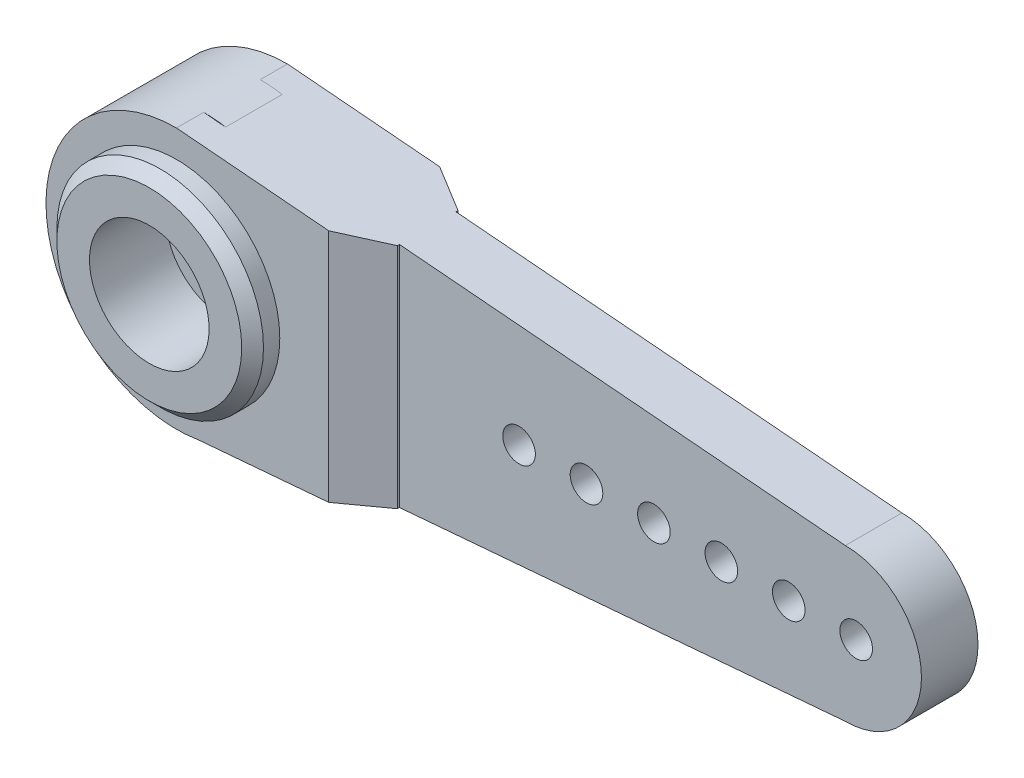
SolidWorks part; units mm, degrees
ref_plane "Front Plane" through (0, 0, 0) normal (0, 0, 1) x (1, 0, 0)
ref_plane "Top Plane" through (0, 0, 0) normal (0, 1, 0) x (1, 0, 0)
ref_plane "Right Plane" through (0, 0, 0) normal (1, 0, 0) x (0, 0, -1)
sketch "Sketch1" plane through (0, 0, 0) normal (0, 0, 1) x (1, 0, 0)
  line L0 (1.0097, 5.9144) -> (29.5, 3.5)
  line L1 (29.5, -3.5) -> (1.0097, -5.9144)
  arc A0 (1.0097, 5.9144) -> (1.0097, -5.9144) centre (0, 0) ccw
  arc A1 (29.5, -3.5) -> (29.5, 3.5) centre (29.5, 0) ccw
  point P5 (-6, 0)
  point P6 (33, 0)
  dimension "D3" = 39
extrude "Boss-Extrude1" add sketch "Sketch1" along normal blind 2.6
sketch "Sketch2" plane through (0, 0, 2.6) normal (0, 0, 1) x (1, 0, 0)
  circle A0 centre (0, 0) radius 4.75
  dimension "D1" = 9.5
extrude "Boss-Extrude2" add sketch "Sketch2" along normal blind 2.5
sketch "Sketch3" plane through (0, 0, 2.6) normal (0, 0, 1) x (1, 0, 0)
  circle A0 centre (0, 0) radius 2.5
  dimension "D1" = 5
extrude "Cut-Extrude1" cut sketch "Sketch3" along normal blind 4
sketch "Sketch4" plane through (0, 0, 2.6) normal (0, 0, 1) x (1, 0, 0)
  line L0 (33, 0) -> (0, 0) construction
  arc A0 (29.5, -3.5) -> (29.5, 3.5) centre (29.5, 0) ccw construction
  circle A1 centre (30, 0) radius 0.75
  circle A3 centre (26.9, 0) radius 0.75
  circle A4 centre (23.8, 0) radius 0.75
  circle A5 centre (20.7, 0) radius 0.75
  circle A6 centre (17.6, 0) radius 0.75
  circle A7 centre (14.5, 0) radius 0.75
  dimension "D1" = 1.5
  dimension "D2" = 3
  dimension "D4" = 3.1
  dimension "D3" = 6
extrude "Cut-Extrude2" cut sketch "Sketch4" against normal blind 4
sketch "Sketch5" plane through (0, 0, 2.6) normal (0, 0, 1) x (1, 0, 0)
  line L0 (0, 6) -> (9, 5.2373)
  line L1 (29.5, 3.5) -> (1.0097, 5.9144) construction
  line L2 (9, 5.2373) -> (9, -5.2373)
  line L3 (1.0097, -5.9144) -> (29.5, -3.5) construction
  line L4 (9, -5.2373) -> (1.0097, -5.9144)
  arc A0 (1.0097, 5.9144) -> (1.0097, -5.9144) centre (0, 0) ccw
  point P7 (8.7819, -5.2558)
  circle M7 centre (0, 0) radius 4.75
  arc M8 (1.0097, 5.9144) -> (1.0097, -5.9144) centre (0, 0) ccw
  line M9 (1.0097, -5.9144) -> (29.5, -3.5)
  line M11 (29.5, 3.5) -> (1.0097, 5.9144)
  dimension "D1" = 9
extrude "Boss-Extrude3" add sketch "Sketch5" along normal blind 1.25 contours L2 L0 M11 M8 M9 M7
chamfer "Chamfer1" distance 2 angle 30 1 edges at (9, 0, 3.85)
sketch "Sketch6" plane through (0, 0, 0) normal (0, 0, -1) x (-1, 0, 0)
  line L0 (0, -6) -> (-9, -5.2373)
  line L1 (-1.0097, -5.9144) -> (-29.5, -3.5) construction
  line L2 (-9, -5.2373) -> (-9, 5.2373)
  line L3 (-29.5, 3.5) -> (-1.0097, 5.9144) construction
  line L4 (-9, 5.2373) -> (0, 6)
  arc A0 (-1.0097, -5.9144) -> (0, 6) centre (0, 0) ccw
  point P1 (0.0183, 6)
  arc M9 (-1.0097, -5.9144) -> (-1.0097, 5.9144) centre (0, 0) ccw
  line M10 (-1.0097, 5.9144) -> (-29.5, 3.5)
  line M12 (-29.5, -3.5) -> (-1.0097, -5.9144)
extrude "Boss-Extrude4" add sketch "Sketch6" along normal blind 1.25 contours L4 L2 L0 M10 M12 M9
chamfer "Chamfer2" distance 2 angle 30 1 edges at (9, 0, -1.25)
sketch "Sketch7" plane through (0, 0, -1.25) normal (0, 0, -1) x (-1, 0, 0)
  line L0 (0, 0) -> (-7, 0) construction
  line L1 (-7, 5.4068) -> (-7, -5.4068) construction
  line L6 (-6.4645, -2.5) -> (-9.4645, -2.5)
  line L7 (-6.4645, -2.5) -> (-6.4645, 2.5)
  line L9 (-7, 0) -> (-33, 0) construction
  line L10 (-9.4645, -2.5) -> (-9.4645, 2.5)
  line L11 (-6.4645, 2.5) -> (-9.4645, 2.5)
  line L12 (-6.4645, -2.5) -> (-9.4645, 2.5) construction
  line L13 (-9.4645, -2.5) -> (-6.4645, 2.5) construction
  arc A0 (-29.5, 3.5) -> (-29.5, -3.5) centre (-29.5, 0) ccw construction
  point P6 (-7, 0)
  point P7 (-8.0126, 0)
  point P8 (0, 0)
  point P9 (-7.7139, 0)
  point P10 (-7.9645, 0)
  point P13 (0, 0)
  point P14 (-6.4645, 2.5)
  dimension "D1" = 5
  dimension "D2" = 3
extrude "Cut-Extrude3" cut sketch "Sketch7" against normal blind 1.25
sketch "Sketch8" plane through (0, 0, 5.1) normal (0, 0, 1) x (1, 0, 0)
  circle A0 centre (0, 0) radius 2.75
  dimension "D1" = 5.5
extrude "Cut-Extrude4" cut sketch "Sketch8" against normal blind 3.5
sketch "Sketch9" plane through (0, 0, -1.25) normal (0, 0, -1) x (-1, 0, 0)
  circle A0 centre (0, 0) radius 3.4
  dimension "D1" = 6.8
extrude "Cut-Extrude5" cut sketch "Sketch9" against normal blind 2
chamfer "Chamfer3" distance 0.5 angle 45 1 edges at (4.75, 0, 5.1)
sketch "Sketch10" plane through (0, 0, 1.6) normal (0, 0, 1) x (1, 0, 0)
  circle A0 centre (0, 0) radius 1.5
  dimension "D1" = 3
extrude "Cut-Extrude6" cut sketch "Sketch10" against normal blind 5
